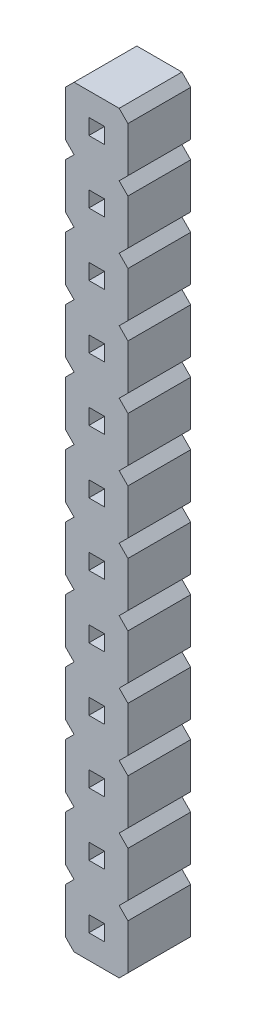
SolidWorks part; units mm, degrees
ref_plane "Alzado" through (0, 0, 0) normal (0, 0, 1) x (1, 0, 0)
ref_plane "Planta" through (0, 0, 0) normal (0, 1, 0) x (1, 0, 0)
ref_plane "Vista lateral" through (0, 0, 0) normal (1, 0, 0) x (0, 0, -1)
sketch "pin_drawing" plane through (0, 0, 0) normal (0, 0, 1) x (1, 0, 0)
  line L0 (0.9381, -1.0393) -> (-0.0144, -1.0393) construction
  line L1 (-0.0144, 2.0791) -> (-0.0144, 0.2531)
  line L2 (-0.0144, -0.4609) -> (-0.0144, -2.2869)
  line L3 (-0.0144, -0.4609) -> (0.3392, -0.1073)
  line L4 (1.5741, -1.6753) -> (2.5183, -1.6753) construction
  line L5 (-0.0144, 2.0791) -> (0.3392, 2.4327)
  line L6 (2.5183, -0.4665) -> (2.5183, -2.2938)
  line L7 (0.9381, -1.3573) -> (0.9381, -1.0393) construction
  line L8 (2.5183, -2.2938) -> (2.1647, -2.6473)
  line L9 (2.1647, -0.1073) -> (2.5183, -0.4665)
  line L10 (1.5741, -1.3573) -> (1.5741, -1.6753) construction
  line L11 (0.3392, -2.6473) -> (-0.0144, -2.2869)
  line L12 (0.9381, -1.0393) -> (1.5741, -1.0393)
  line L13 (0.9381, -1.0393) -> (0.9381, -1.6753)
  line L14 (0.9381, -1.6753) -> (1.5741, -1.6753)
  line L15 (1.5741, -1.0393) -> (1.5741, -1.6753)
  line L16 (2.5183, 2.0735) -> (2.5183, 0.2462)
  line L17 (2.5183, 0.2462) -> (2.1647, -0.1073)
  line L18 (2.1647, 2.4327) -> (2.5183, 2.0735)
  line L19 (0.3392, -0.1073) -> (-0.0144, 0.2531)
  line L20 (0.9381, 1.5007) -> (1.5741, 1.5007)
  line L21 (0.9381, 1.5007) -> (0.9381, 0.8647)
  line L22 (0.9381, 0.8647) -> (1.5741, 0.8647)
  line L23 (1.5741, 1.5007) -> (1.5741, 0.8647)
  line L24 (0.9381, 1.5007) -> (-0.0144, 1.5007) construction
  line L25 (1.5741, 0.8647) -> (2.5183, 0.8647) construction
  line L26 (0.9381, 1.1827) -> (0.9381, 1.5007) construction
  line L27 (1.5741, 1.1827) -> (1.5741, 0.8647) construction
  line L28 (-0.0144, 4.6191) -> (-0.0144, 2.7931)
  line L29 (-0.0144, 4.6191) -> (0.3392, 4.9727)
  line L30 (2.5183, 4.6135) -> (2.5183, 2.7862)
  line L31 (2.5183, 2.7862) -> (2.1647, 2.4327)
  line L32 (2.1647, 4.9727) -> (2.5183, 4.6135)
  line L33 (0.3392, 2.4327) -> (-0.0144, 2.7931)
  line L34 (0.9381, 4.0407) -> (1.5741, 4.0407)
  line L35 (0.9381, 4.0407) -> (0.9381, 3.4047)
  line L36 (0.9381, 3.4047) -> (1.5741, 3.4047)
  line L37 (1.5741, 4.0407) -> (1.5741, 3.4047)
  line L38 (0.9381, 4.0407) -> (-0.0144, 4.0407) construction
  line L39 (1.5741, 3.4047) -> (2.5183, 3.4047) construction
  line L40 (0.9381, 3.7227) -> (0.9381, 4.0407) construction
  line L41 (1.5741, 3.7227) -> (1.5741, 3.4047) construction
  line L42 (-0.0144, 7.1591) -> (-0.0144, 5.3331)
  line L43 (-0.0144, 7.1591) -> (0.3392, 7.5127)
  line L44 (2.5183, 7.1535) -> (2.5183, 5.3262)
  line L45 (2.5183, 5.3262) -> (2.1647, 4.9727)
  line L46 (2.1647, 7.5127) -> (2.5183, 7.1535)
  line L47 (0.3392, 4.9727) -> (-0.0144, 5.3331)
  line L48 (0.9381, 6.5807) -> (1.5741, 6.5807)
  line L49 (0.9381, 6.5807) -> (0.9381, 5.9447)
  line L50 (0.9381, 5.9447) -> (1.5741, 5.9447)
  line L51 (1.5741, 6.5807) -> (1.5741, 5.9447)
  line L52 (0.9381, 6.5807) -> (-0.0144, 6.5807) construction
  line L53 (1.5741, 5.9447) -> (2.5183, 5.9447) construction
  line L54 (0.9381, 6.2627) -> (0.9381, 6.5807) construction
  line L55 (1.5741, 6.2627) -> (1.5741, 5.9447) construction
  line L56 (-0.0144, 9.6991) -> (-0.0144, 7.8731)
  line L57 (-0.0144, 9.6991) -> (0.3392, 10.0527)
  line L58 (2.5183, 9.6935) -> (2.5183, 7.8662)
  line L59 (2.5183, 7.8662) -> (2.1647, 7.5127)
  line L60 (2.1647, 10.0527) -> (2.5183, 9.6935)
  line L61 (0.3392, 7.5127) -> (-0.0144, 7.8731)
  line L62 (0.9381, 9.1207) -> (1.5741, 9.1207)
  line L63 (0.9381, 9.1207) -> (0.9381, 8.4847)
  line L64 (0.9381, 8.4847) -> (1.5741, 8.4847)
  line L65 (1.5741, 9.1207) -> (1.5741, 8.4847)
  line L66 (0.9381, 9.1207) -> (-0.0144, 9.1207) construction
  line L67 (1.5741, 8.4847) -> (2.5183, 8.4847) construction
  line L68 (0.9381, 8.8027) -> (0.9381, 9.1207) construction
  line L69 (1.5741, 8.8027) -> (1.5741, 8.4847) construction
  line L70 (-0.0144, 12.2391) -> (-0.0144, 10.4131)
  line L71 (-0.0144, 12.2391) -> (0.3392, 12.5927)
  line L72 (2.5183, 12.2335) -> (2.5183, 10.4062)
  line L73 (2.5183, 10.4062) -> (2.1647, 10.0527)
  line L74 (2.1647, 12.5927) -> (2.5183, 12.2335)
  line L75 (0.3392, 10.0527) -> (-0.0144, 10.4131)
  line L76 (0.9381, 11.6607) -> (1.5741, 11.6607)
  line L77 (0.9381, 11.6607) -> (0.9381, 11.0247)
  line L78 (0.9381, 11.0247) -> (1.5741, 11.0247)
  line L79 (1.5741, 11.6607) -> (1.5741, 11.0247)
  line L80 (0.9381, 11.6607) -> (-0.0144, 11.6607) construction
  line L81 (1.5741, 11.0247) -> (2.5183, 11.0247) construction
  line L82 (0.9381, 11.3427) -> (0.9381, 11.6607) construction
  line L83 (1.5741, 11.3427) -> (1.5741, 11.0247) construction
  line L84 (-0.0144, 14.7791) -> (-0.0144, 12.9531)
  line L85 (-0.0144, 14.7791) -> (0.3392, 15.1327)
  line L86 (2.5183, 14.7735) -> (2.5183, 12.9462)
  line L87 (2.5183, 12.9462) -> (2.1647, 12.5927)
  line L88 (2.1647, 15.1327) -> (2.5183, 14.7735)
  line L89 (0.3392, 12.5927) -> (-0.0144, 12.9531)
  line L90 (0.9381, 14.2007) -> (1.5741, 14.2007)
  line L91 (0.9381, 14.2007) -> (0.9381, 13.5647)
  line L92 (0.9381, 13.5647) -> (1.5741, 13.5647)
  line L93 (1.5741, 14.2007) -> (1.5741, 13.5647)
  line L94 (0.9381, 14.2007) -> (-0.0144, 14.2007) construction
  line L95 (1.5741, 13.5647) -> (2.5183, 13.5647) construction
  line L96 (0.9381, 13.8827) -> (0.9381, 14.2007) construction
  line L97 (1.5741, 13.8827) -> (1.5741, 13.5647) construction
  line L98 (-0.0144, 17.3191) -> (-0.0144, 15.4931)
  line L99 (-0.0144, 17.3191) -> (0.3392, 17.6727)
  line L100 (2.5183, 17.3135) -> (2.5183, 15.4862)
  line L101 (2.5183, 15.4862) -> (2.1647, 15.1327)
  line L102 (2.1647, 17.6727) -> (2.5183, 17.3135)
  line L103 (0.3392, 15.1327) -> (-0.0144, 15.4931)
  line L104 (0.9381, 16.7407) -> (1.5741, 16.7407)
  line L105 (0.9381, 16.7407) -> (0.9381, 16.1047)
  line L106 (0.9381, 16.1047) -> (1.5741, 16.1047)
  line L107 (1.5741, 16.7407) -> (1.5741, 16.1047)
  line L108 (0.9381, 16.7407) -> (-0.0144, 16.7407) construction
  line L109 (1.5741, 16.1047) -> (2.5183, 16.1047) construction
  line L110 (0.9381, 16.4227) -> (0.9381, 16.7407) construction
  line L111 (1.5741, 16.4227) -> (1.5741, 16.1047) construction
  line L112 (-0.0144, 19.8591) -> (-0.0144, 18.0331)
  line L113 (-0.0144, 19.8591) -> (0.3392, 20.2127)
  line L114 (2.5183, 19.8535) -> (2.5183, 18.0262)
  line L115 (2.5183, 18.0262) -> (2.1647, 17.6727)
  line L116 (2.1647, 20.2127) -> (2.5183, 19.8535)
  line L117 (0.3392, 17.6727) -> (-0.0144, 18.0331)
  line L118 (0.9381, 19.2807) -> (1.5741, 19.2807)
  line L119 (0.9381, 19.2807) -> (0.9381, 18.6447)
  line L120 (0.9381, 18.6447) -> (1.5741, 18.6447)
  line L121 (1.5741, 19.2807) -> (1.5741, 18.6447)
  line L122 (0.9381, 19.2807) -> (-0.0144, 19.2807) construction
  line L123 (1.5741, 18.6447) -> (2.5183, 18.6447) construction
  line L124 (0.9381, 18.9627) -> (0.9381, 19.2807) construction
  line L125 (1.5741, 18.9627) -> (1.5741, 18.6447) construction
  line L126 (-0.0144, 22.3991) -> (-0.0144, 20.5731)
  line L127 (-0.0144, 22.3991) -> (0.3392, 22.7527)
  line L128 (2.5183, 22.3935) -> (2.5183, 20.5662)
  line L129 (2.5183, 20.5662) -> (2.1647, 20.2127)
  line L130 (2.1647, 22.7527) -> (2.5183, 22.3935)
  line L131 (0.3392, 20.2127) -> (-0.0144, 20.5731)
  line L132 (0.9381, 21.8207) -> (1.5741, 21.8207)
  line L133 (0.9381, 21.8207) -> (0.9381, 21.1847)
  line L134 (0.9381, 21.1847) -> (1.5741, 21.1847)
  line L135 (1.5741, 21.8207) -> (1.5741, 21.1847)
  line L136 (0.9381, 21.8207) -> (-0.0144, 21.8207) construction
  line L137 (1.5741, 21.1847) -> (2.5183, 21.1847) construction
  line L138 (0.9381, 21.5027) -> (0.9381, 21.8207) construction
  line L139 (1.5741, 21.5027) -> (1.5741, 21.1847) construction
  line L140 (-0.0144, 24.9391) -> (-0.0144, 23.1131)
  line L141 (-0.0144, 24.9391) -> (0.3392, 25.2927)
  line L142 (2.5183, 24.9335) -> (2.5183, 23.1062)
  line L143 (2.5183, 23.1062) -> (2.1647, 22.7527)
  line L144 (2.1647, 25.2927) -> (2.5183, 24.9335)
  line L145 (0.3392, 22.7527) -> (-0.0144, 23.1131)
  line L146 (0.9381, 24.3607) -> (1.5741, 24.3607)
  line L147 (0.9381, 24.3607) -> (0.9381, 23.7247)
  line L148 (0.9381, 23.7247) -> (1.5741, 23.7247)
  line L149 (1.5741, 24.3607) -> (1.5741, 23.7247)
  line L150 (0.9381, 24.3607) -> (-0.0144, 24.3607) construction
  line L151 (1.5741, 23.7247) -> (2.5183, 23.7247) construction
  line L152 (0.9381, 24.0427) -> (0.9381, 24.3607) construction
  line L153 (1.5741, 24.0427) -> (1.5741, 23.7247) construction
  line L154 (-0.0144, 27.4791) -> (-0.0144, 25.6531)
  line L155 (-0.0144, 27.4791) -> (0.3392, 27.8327)
  line L156 (2.5183, 27.4735) -> (2.5183, 25.6462)
  line L157 (2.5183, 25.6462) -> (2.1647, 25.2927)
  line L158 (2.1647, 27.8327) -> (2.5183, 27.4735)
  line L159 (0.3392, 25.2927) -> (-0.0144, 25.6531)
  line L160 (0.9381, 26.9007) -> (1.5741, 26.9007)
  line L161 (0.9381, 26.9007) -> (0.9381, 26.2647)
  line L162 (0.9381, 26.2647) -> (1.5741, 26.2647)
  line L163 (1.5741, 26.9007) -> (1.5741, 26.2647)
  line L164 (0.9381, 26.9007) -> (-0.0144, 26.9007) construction
  line L165 (1.5741, 26.2647) -> (2.5183, 26.2647) construction
  line L166 (0.9381, 26.5827) -> (0.9381, 26.9007) construction
  line L167 (1.5741, 26.5827) -> (1.5741, 26.2647) construction
  line L168 (2.1647, -2.6473) -> (0.3392, -2.6473)
  line L169 (0.3392, 27.8327) -> (2.1647, 27.8327)
  dimension "D1" = 0.318
  dimension "D2" = 0.9525
  dimension "D3" = 0.5
  dimension "D4" = 135
  dimension "D5" = 0.5
  dimension "D6" = 135
  dimension "D7" = 12
  dimension "D8" = 2.54
extrude "Boss-Extrude1" add sketch "pin_drawing" along normal blind 2.54
